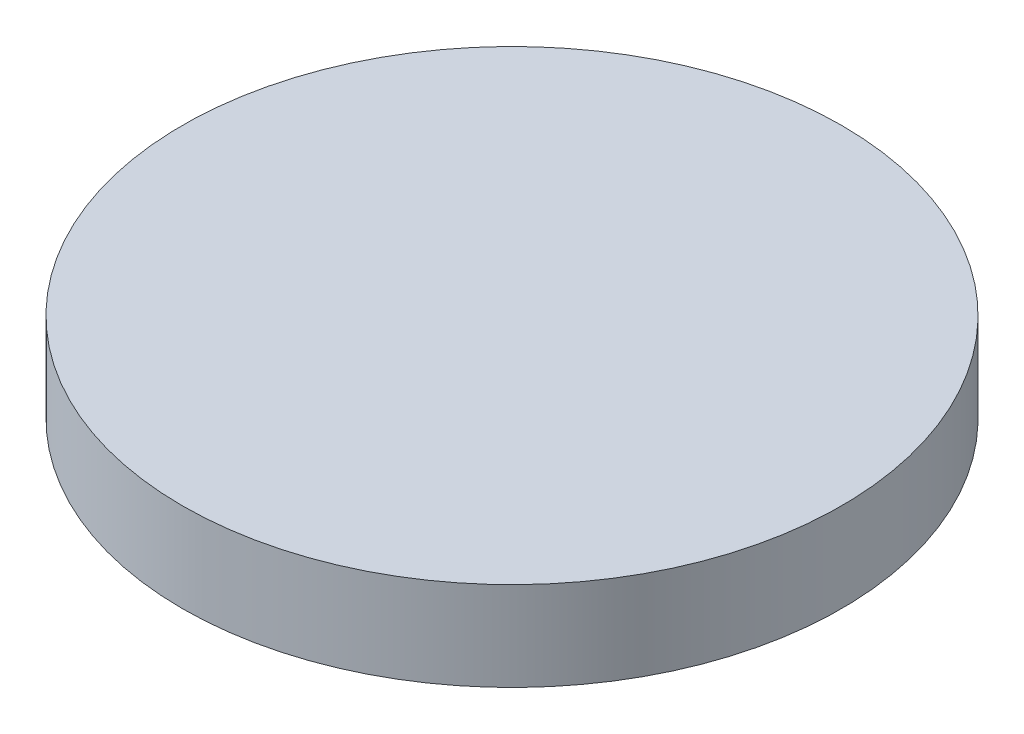
SolidWorks part; units mm, degrees
ref_plane "Front Plane" through (0, 0, 0) normal (0, 0, 1) x (1, 0, 0)
ref_plane "Top Plane" through (0, 0, 0) normal (0, 1, 0) x (1, 0, 0)
ref_plane "Right Plane" through (0, 0, 0) normal (1, 0, 0) x (0, 0, -1)
sketch "Sketch1" plane through (0, 0, 0) normal (0, 1, 0) x (1, 0, 0)
  circle A0 centre (-140.1164, 35.1898) radius 37
extrude "Boss-Extrude1" add sketch "Sketch1" along normal blind 10
